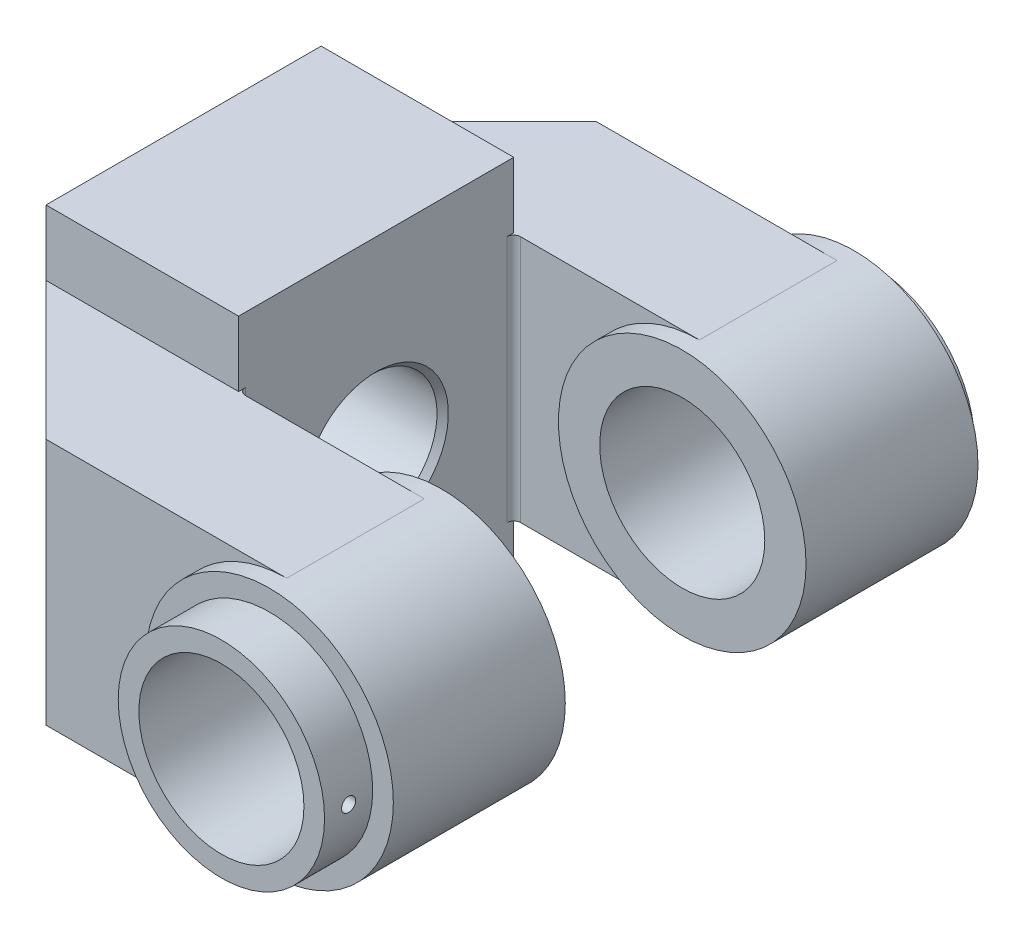
SolidWorks part; units mm, degrees
material "Сталь"
ref_plane "Спереди" through (0, 0, 0) normal (0, 0, 1) x (1, 0, 0)
ref_plane "Сверху" through (0, 0, 0) normal (0, 1, 0) x (1, 0, 0)
ref_plane "Справа" through (0, 0, 0) normal (1, 0, 0) x (0, 0, -1)
sketch "Эскиз1" plane through (0, 0, 0) normal (0, 0, 1) x (1, 0, 0)
  line L1 (-28, -55) -> (28, -55)
  line L2 (-28, -55) -> (-28, 55)
  line L3 (-28, 55) -> (28, 55)
  line L4 (28, -55) -> (28, 55)
  line L5 (-28, -55) -> (28, 55) construction
  line L6 (-28, 55) -> (28, -55) construction
  point P0 (0, 0)
  dimension "D1" = 56
  dimension "D2" = 110
extrude "Бобышка-Вытянуть1" add sketch "Эскиз1" along normal blind 40
sketch "Эскиз3" plane through (0, 0, 40) normal (0, 0, 1) x (1, 0, 0)
  line L0 (-28, 55) -> (-28, -55) construction
  line L1 (-28, -36) -> (82, -36)
  line L2 (-28, -36) -> (-28, 36)
  line L3 (-28, 36) -> (82, 36)
  line L4 (82, -36) -> (82, 36)
  line L5 (-28, -36) -> (82, 36) construction
  line L6 (-28, 36) -> (82, -36) construction
  circle A0 centre (82, 0) radius 36
  circle A1 centre (82, 0) radius 24
  point P0 (27, 0)
  line M1 (28, -55) -> (28, 55)
  line M3 (-28, 55) -> (-28, -55)
  dimension "D3" = 48
  dimension "D1" = 72
  dimension "D2" = 110
extrude "Бобышка-Вытянуть2" add sketch "Эскиз3" along normal blind 40 contours L3 L1 M3 M1 | A0 L3 L1 M1 | A1 L4 A0 | A1 L4 A0
ref_plane "Плоскость1" through (0, 0, 60) normal (0, 0, 1) x (1, 0, 0)
sketch "Эскиз4" plane through (0, 0, 60) normal (0, 0, 1) x (1, 0, 0)
  circle A0 centre (82, 0) radius 36
  circle A1 centre (82, 0) radius 24 construction
  circle A2 centre (82, 0) radius 24
  arc A3 (82, -36) -> (82, 36) centre (82, 0) ccw construction
extrude "Бобышка-Вытянуть3" add sketch "Эскиз4" along normal mid plane 50
sketch "Эскиз5" plane through (0, 0, 85) normal (0, 0, 1) x (1, 0, 0)
  circle A0 centre (82, 0) radius 30
  circle A1 centre (82, 0) radius 24 construction
  circle A2 centre (82, 0) radius 24
  dimension "D1" = 60
extrude "Бобышка-Вытянуть4" add sketch "Эскиз5" along normal blind 5
chamfer "Фаска1" distance 40 angle 45 1 edges at (-28, 0, 80)
fillet "Скругление1" radius 2 1 edges at (28, 0, 40)
mirror "Зеркальное отражение1" about plane through (0, 0, 0) normal (0, 0, -1) of bodies 108
sketch "Эскиз6" plane through (-28, 0, 0) normal (-1, 0, 0) x (0, 0, 1)
  circle A0 centre (0, 0) radius 19.352
  dimension "D1" = 38.704
extrude "Вырез-Вытянуть1" cut sketch "Эскиз6" against normal through all
cosmetic thread "Условное изображение резьбы1" parameters "D2"=42
chamfer "Фаска2" distance 1.648 angle 45 2 edges at (28, 0, 19.352) (-28, 0, 19.352)
sketch "Эскиз7" plane through (0, 0, 90) normal (0, 0, 1) x (1, 0, 0)
  circle A0 centre (82, 0) radius 24 construction
  circle A1 centre (82, 0) radius 30
  circle A2 centre (82, 0) radius 30
  circle A3 centre (82, 0) radius 24
  dimension "D1" = 0
extrude "Бобышка-Вытянуть5" add sketch "Эскиз7" along normal blind 9
ref_plane "Плоскость2" through (82, 0, 0) normal (1, 0, 0) x (0, 0, -1)
sketch "Эскиз8" plane through (82, 0, 0) normal (1, 0, 0) x (0, 0, -1)
  line L0 (-99, 0) -> (-85, 0) construction
  line L1 (-99, 30) -> (-99, -30) construction
  line L2 (-85, 36) -> (-85, -36) construction
  circle A0 centre (-92, 0) radius 2.05
  dimension "D1" = 4.1
extrude "Вырез-Вытянуть2" cut sketch "Эскиз8" along normal through all
